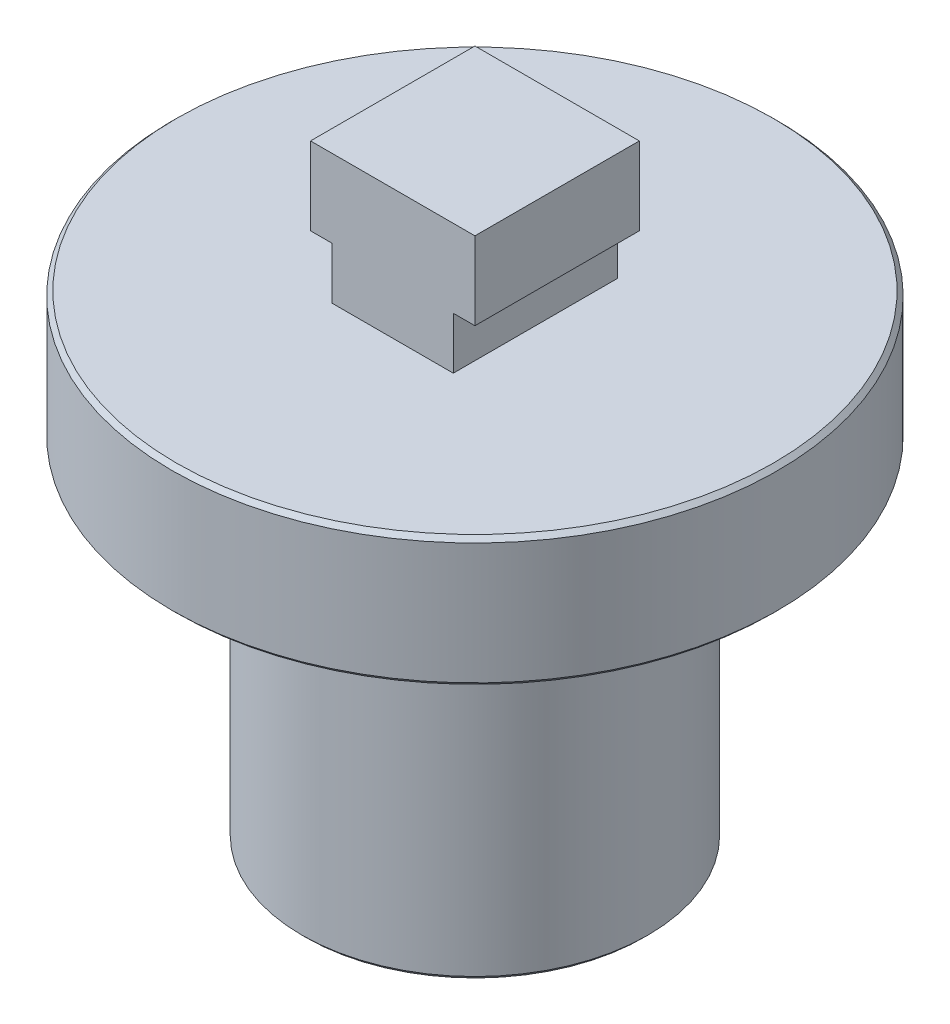
SolidWorks part; units mm, degrees
ref_plane "정면" through (0, 0, 0) normal (0, 0, 1) x (1, 0, 0)
ref_plane "윗면" through (0, 0, 0) normal (0, 1, 0) x (1, 0, 0)
ref_plane "우측면" through (0, 0, 0) normal (1, 0, 0) x (0, 0, -1)
sketch "Sketch1" plane through (0, 0, 0) normal (0, 1, 0) x (1, 0, 0)
  circle A0 centre (0, 0) radius 4
  dimension "D1" = 8
extrude "Boss-Extrude1" add sketch "Sketch1" along normal blind 11
sketch "Sketch2" plane through (0, 0, 0) normal (0, -1, 0) x (1, 0, 0)
  line L1 (-1.9, -1.9) -> (1.9, -1.9)
  line L2 (-1.9, -1.9) -> (-1.9, 1.9)
  line L3 (-1.9, 1.9) -> (1.9, 1.9)
  line L4 (1.9, -1.9) -> (1.9, 1.9)
  line L5 (-1.9, -1.9) -> (1.9, 1.9) construction
  line L6 (-1.9, 1.9) -> (1.9, -1.9) construction
  point P0 (0, 0)
  dimension "D1" = 3.8
  dimension "D2" = 3.8
extrude "Cut-Extrude1" cut sketch "Sketch2" against normal blind 4
sketch "Sketch3" plane through (0, 11, 0) normal (0, 1, 0) x (1, 0, 0)
  line L1 (-1.9, -1.9) -> (1.9, -1.9)
  line L2 (-1.9, -1.9) -> (-1.9, 1.9)
  line L3 (-1.9, 1.9) -> (1.9, 1.9)
  line L4 (1.9, -1.9) -> (1.9, 1.9)
  line L5 (-1.9, -1.9) -> (1.9, 1.9) construction
  line L6 (-1.9, 1.9) -> (1.9, -1.9) construction
  point P0 (0, 0)
  dimension "D1" = 3.8
  dimension "D2" = 3.8
extrude "Boss-Extrude2" add sketch "Sketch3" along normal blind 3
sketch "Sketch4" plane through (0, 0, 1.9) normal (0, 0, 1) x (1, 0, 0)
  line L1 (-1.9, 11) -> (-1.4, 11)
  line L2 (-1.9, 11) -> (-1.9, 12.2)
  line L3 (-1.9, 12.2) -> (-1.4, 12.2)
  line L4 (-1.4, 11) -> (-1.4, 12.2)
  line L5 (1.9, 11) -> (1.4, 11)
  line L6 (1.9, 11) -> (1.9, 12.2)
  line L7 (1.9, 12.2) -> (1.4, 12.2)
  line L8 (1.4, 11) -> (1.4, 12.2)
  dimension "D1" = 0.5
  dimension "D2" = 0.5
  dimension "D3" = 1.2
  dimension "D4" = 1.2
extrude "Cut-Extrude2" cut sketch "Sketch4" against normal blind 13
sketch "Sketch5" plane through (0, 11, 0) normal (0, 1, 0) x (1, 0, 0)
  circle A0 centre (0, 0) radius 7
  dimension "D1" = 14
extrude "Boss-Extrude3" add sketch "Sketch5" against normal blind 3
chamfer "Chamfer1" distance 0.1 angle 45 3 edges at (0, 0, 4) (0, 8, 7) (0, 11, 7)
